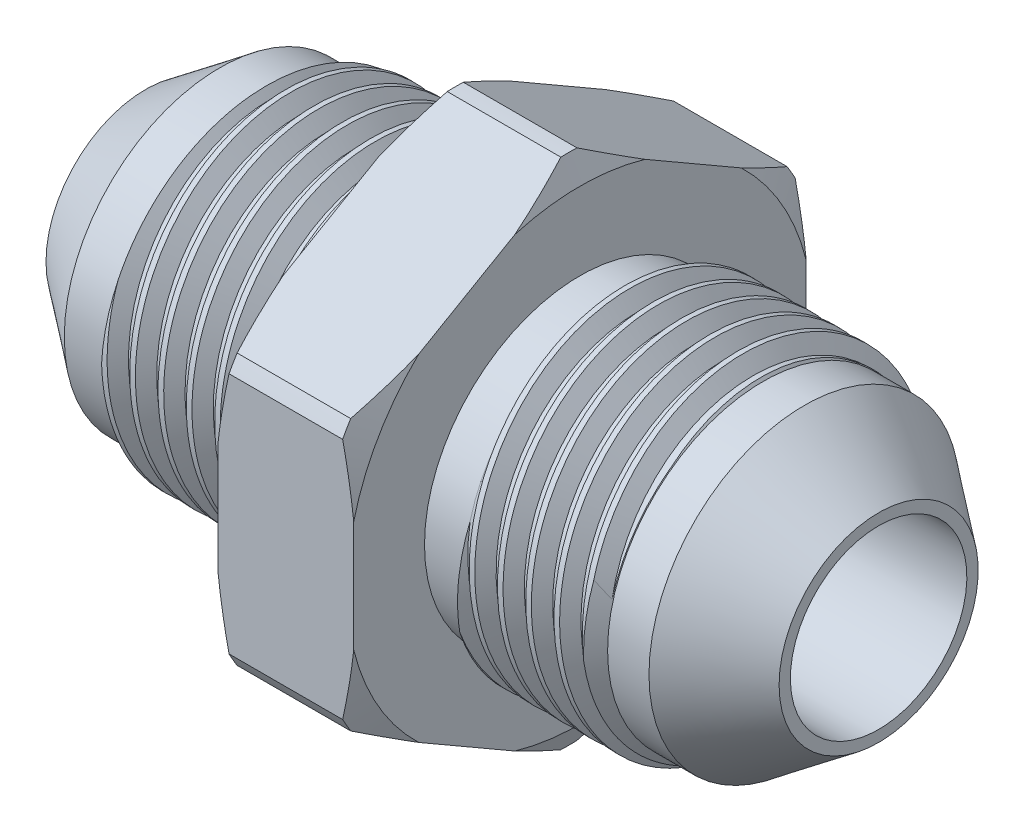
SolidWorks part; units mm, degrees
material "Cast Stainless Steel"
ref_plane "Front" through (0, 0, 0) normal (0, 0, 1) x (1, 0, 0)
ref_plane "Top" through (0, 0, 0) normal (0, 1, 0) x (1, 0, 0)
ref_plane "Right" through (0, 0, 0) normal (1, 0, 0) x (0, 0, -1)
sketch "Sketch6" plane through (0, 0, 0) normal (0, 0, 1) x (1, 0, 0)
  line L1 (20.574, 9.525) -> (20.574, -9.525) construction
  line L2 (-20.574, 0) -> (20.574, 0)
  line L4 (-20.574, 0) -> (-20.574, 9.525)
  line L5 (-20.574, 9.525) -> (20.574, 9.525)
  line L6 (20.574, 0) -> (20.574, 9.525)
  point P4 (3.81, 0)
  point P6 (-3.81, 0)
  dimension "D1" = 16.764
  dimension "Straight Dia" = 19.05
  dimension "Length" = 41.148
  dimension "L1" = 16.764
revolve "Revolve3" add sketch "Sketch6" angle 360 about L2
sketch "Sketch9" plane through (0, 0, 0) normal (0, 0, 1) x (1, 0, 0)
  line L0 (-20.574, 9.525) -> (-20.574, -9.525) construction
  line L1 (-20.574, -9.525) -> (-18.9865, -9.525) construction
  line L3 (-18.9865, -9.525) -> (-20.574, 9.525) construction
  line L4 (-20.574, 9.525) -> (-20.3762, 9.5415) construction
  line L5 (-20.3762, 9.5415) -> (-18.992, 9.6568)
  line L6 (-20.574, 0) -> (-20.574, 9.525) construction
  line L7 (-20.3762, 9.5415) -> (-19.8105, 8.7264)
  line L8 (-19.8105, 8.7264) -> (-19.415, 8.7593)
  line L9 (-19.415, 8.7593) -> (-18.992, 9.6568)
  line L10 (-19.6128, 8.7429) -> (-19.6841, 9.5992) construction
  line L11 (-18.0904, -9.525) -> (-19.6779, 9.525) construction
  line L12 (-20.574, 9.525) -> (20.574, 9.525) construction
  line L13 (-20.574, -0.1408) -> (-17.1944, 0.1408) construction
  point P19 (-18.8842, 0)
  point P20 (-18.8842, 0)
  dimension "D1" = 1.5875
  dimension "Straight Pitch" = 1.5875
  dimension "D2" = 0.1984
  dimension "D3" = 60
  dimension "D4" = 0.3969
revolve "Cut-Revolve4" cut sketch "Sketch9" angle 360 about L13
pattern_linear "LPattern4" count 26 spacing 1.5875 along (1, 0, 0) count 2 spacing 1.5875 along (-1, 0, 0) of "Cut-Revolve4"
ref_plane "Plane1" through (-3.81, 0, 0) normal (1, 0, 0) x (0, 0, -1)
sketch "Sketch12" plane through (-3.81, 0, 0) normal (1, 0, 0) x (0, 0, -1)
  line L1 (0, 14.6647) -> (-12.7, 7.3323)
  line L2 (-12.7, 7.3323) -> (-12.7, -7.3323)
  line L3 (-12.7, -7.3323) -> (0, -14.6647)
  line L4 (0, -14.6647) -> (12.7, -7.3323)
  line L5 (12.7, -7.3323) -> (12.7, 7.3323)
  line L6 (12.7, 7.3323) -> (0, 14.6647)
  circle A0 centre (0, 0) radius 12.7 construction
  dimension "Hex" = 25.4
extrude "Extrude1" add sketch "Sketch12" along normal up to vertex (7.62 mm away) up to point (3.81, 0, 0)
sketch "Sketch7" plane through (0, 0, 0) normal (0, 0, 1) x (1, 0, 0)
  line L0 (-20.574, 0) -> (-20.574, 4.953)
  line L2 (-20.574, 4.953) -> (20.574, 4.953)
  line L4 (20.574, 0) -> (20.574, 9.525) construction
  line L11 (20.574, 4.953) -> (20.574, 0)
  line L12 (20.574, 0) -> (-20.574, 0)
  line L13 (-20.574, 4.953) -> (-20.574, -4.953) construction
  dimension "ID" = 9.906
revolve "Cut-Revolve5" cut sketch "Sketch7" angle 360 about L12
sketch "Sketch10" plane through (0, 0, 0) normal (0, 0, 1) x (1, 0, 0)
  line L0 (13.5331, 9.525) -> (13.5331, 8.7264) construction
  line L1 (-20.574, 9.525) -> (20.574, 9.525) construction
  line L2 (13.5331, 8.7264) -> (16.4092, 8.7264) construction
  line L3 (-13.5331, 9.525) -> (-13.5331, 8.7264) construction
  line L4 (20.574, 5.588) -> (20.574, 9.525)
  line L5 (20.574, 9.525) -> (13.5331, 9.525)
  line L6 (16.4092, 8.7264) -> (20.574, 5.588)
  line L7 (20.574, 4.953) -> (20.574, 9.525) construction
  line L8 (13.5331, 9.525) -> (14.0874, 8.7264)
  line L9 (14.0874, 8.7264) -> (16.4092, 8.7264)
  line L10 (-20.3762, 9.5415) -> (-19.8105, 8.7264) construction
  line L11 (-13.5331, 8.7264) -> (-16.4092, 8.7264) construction
  line L12 (-20.574, 4.953) -> (-20.574, -4.953) construction
  line L13 (-20.574, 5.588) -> (-20.574, 9.525)
  line L14 (-16.4092, 8.7264) -> (-20.574, 5.588)
  line L15 (-14.0874, 8.7264) -> (-16.4092, 8.7264)
  line L16 (-13.5331, 9.525) -> (-14.0874, 8.7264)
  line L17 (-20.574, 9.525) -> (-13.5331, 9.525)
  dimension "D1" = 37
  dimension "D2" = 7.0409
  dimension "D3" = 0.635
  dimension "D4" = 37
revolve "Cut-Revolve6" cut sketch "Sketch10" angle 360 about L2
sketch "Sketch13" plane through (0, 0, 0) normal (0, 0, 1) x (1, 0, 0)
  line L0 (-3.81, 14.6647) -> (-3.81, 13.0772)
  line L1 (-3.81, 7.3323) -> (-3.81, 14.6647) construction
  line L2 (-3.81, 13.0772) -> (-3.1882, 14.4107)
  line L3 (-3.1882, 14.4107) -> (3.1882, 14.4107)
  line L4 (3.1882, 14.4107) -> (3.81, 13.0772)
  line L5 (3.81, 14.6647) -> (3.81, 7.3323) construction
  line L6 (3.81, 13.0772) -> (3.81, 14.6647)
  line L7 (3.81, 14.6647) -> (-3.81, 14.6647)
  dimension "D1" = 1.5875
  dimension "D2" = 25
  dimension "D3" = 0.254
revolve "Cut-Revolve7" cut sketch "Sketch13" angle 360 about L2
sketch "Sketch11" plane through (0, 0, 0) normal (0, 0, 1) x (1, 0, 0)
  line L0 (14.0874, 8.7264) -> (16.4092, 8.7264) construction
  line L1 (-6.1318, 8.7264) -> (-3.81, 8.7264)
  line L2 (-6.1318, 8.7264) -> (-6.1318, 11.2664)
  line L3 (-6.1318, 11.2664) -> (-3.81, 11.2664)
  line L4 (-3.81, 8.7264) -> (-3.81, 11.2664)
  line L5 (3.81, 12.5576) -> (3.81, 13.0772) construction
  line L7 (-3.81, 7.3323) -> (-3.81, 14.6647) construction
  line L10 (3.81, 8.7264) -> (6.1318, 8.7264)
  line L11 (3.81, 8.7264) -> (3.81, 11.2664)
  line L12 (3.81, 11.2664) -> (6.1318, 11.2664)
  line L13 (6.1318, 8.7264) -> (6.1318, 11.2664)
  dimension "D1" = 2.54
revolve "Cut-Revolve9" cut sketch "Sketch11" angle 360 about L2
sketch "Sketch14" plane through (0, 0, 0) normal (0, 0, 1) x (1, 0, 0)
  line L0 (-3.81, 9.525) -> (-3.81, -9.525) construction
  line L1 (-24.638, 8.7264) -> (-20.447, 8.7264)
  line L2 (-24.638, 8.7264) -> (-24.638, 18.8864)
  line L3 (-24.638, 18.8864) -> (-20.447, 18.8864)
  line L4 (-20.447, 8.7264) -> (-20.447, 18.8864)
  line L5 (33.1261, 0) -> (-33.0585, 0) construction
  line L9 (-16.4092, -8.7264) -> (-16.4092, 8.7264) construction
  line L10 (-16.4092, 8.7264) -> (-16.4092, -8.7264) construction
  line L11 (-16.4092, 8.7264) -> (-24.638, 8.7264) construction
  point P13 (-16.4092, 0)
  dimension "D1" = 16.637
  dimension "D2" = 4.191
  dimension "D3" = 10.16
revolve "Cut-Revolve8" [suppressed] cut sketch "Sketch14" angle 360 about L5
equation "\"D1@Sketch9\" = \"Straight Pitch@Sketch9\""
equation "\"D2@Sketch9\" = \"Straight Pitch@Sketch9\"/8"
equation "\"D4@Sketch9\" = \"Straight Pitch@Sketch9\"/4"
equation "\"D3@LPattern4\" = \"Straight Pitch@Sketch9\""
equation "\"D4@LPattern4\" = \"D3@LPattern4\""
equation "\"D1@LPattern4\" = \"Length@Sketch6\"/\"Straight Pitch@Sketch9\""
equation "\"D2@Sketch10\" = \"L1@Sketch6\"*(4.2/10)"
